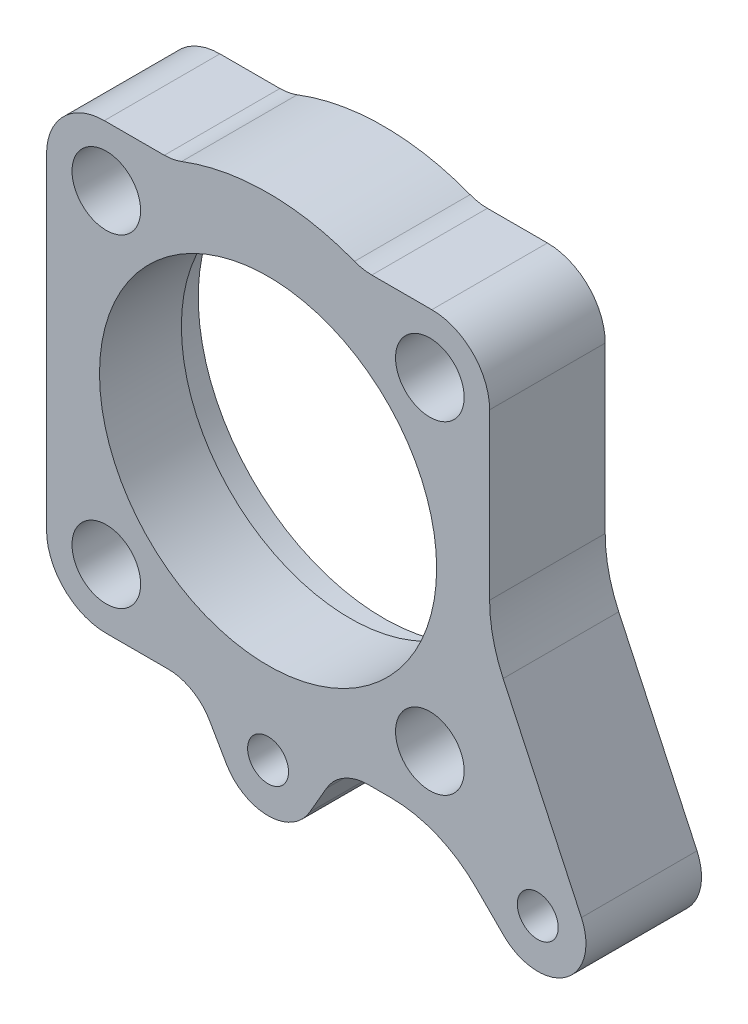
SolidWorks part; units mm, degrees
ref_plane "Front" through (0, 0, 0) normal (0, 0, 1) x (1, 0, 0)
ref_plane "Top" through (0, 0, 0) normal (0, 1, 0) x (1, 0, 0)
ref_plane "Right" through (0, 0, 0) normal (1, 0, 0) x (0, 0, -1)
sketch "Sketch1" plane through (0, 0, 0) normal (0, 0, 1) x (1, 0, 0)
  line L0 (-25.5577, 0) -> (31, 0) construction
  line L1 (0, 61.8389) -> (0, -52) construction
  line L2 (34, 46) -> (21.5407, 46)
  line L3 (46, 34) -> (46, -0.2421)
  line L4 (-33.5876, -46) -> (-20.7846, -46)
  line L5 (0, 0) -> (33.5876, 33.5876) construction
  line L6 (48.9289, -59.0711) -> (43.1802, -53.3223)
  line L7 (65.0631, -47.7738) -> (48.8108, -12.9206)
  line L9 (-46, -33.5876) -> (-46, 0)
  line L10 (8.6603, -57) -> (12.1244, -51)
  line L11 (-46, 34) -> (-46, 0)
  line L12 (-34, 46) -> (-21.5407, 46)
  line L13 (25.5025, -46) -> (20.7846, -46)
  line L14 (-8.6603, -57) -> (-12.1244, -51)
  circle A0 centre (0, 0) radius 31
  arc A1 (17.9505, 46.6667) -> (-17.9505, 46.6667) centre (0, 0) ccw
  arc A2 (8.6603, -57) -> (-8.6603, -57) centre (0, -52) cw
  arc A3 (65.0631, -47.7738) -> (48.9289, -59.0711) centre (56, -52) cw
  circle A4 centre (0, 0) radius 47.5 construction
  circle A5 centre (33.5876, 33.5876) radius 7.125 construction
  arc A6 (46, 34) -> (34, 46) centre (34, 34) ccw
  arc A7 (17.9505, 46.6667) -> (21.5407, 46) centre (21.5407, 56) ccw
  arc A8 (25.5025, -46) -> (43.1802, -53.3223) centre (25.5025, -71) cw
  arc A9 (-46, -33.5876) -> (-33.5876, -46) centre (-33.5876, -33.5876) ccw
  circle A10 centre (33.5876, -33.5876) radius 7.125 construction
  arc A11 (46, -0.2421) -> (48.8108, -12.9206) centre (76, -0.2421) ccw
  arc A13 (20.7846, -46) -> (12.1244, -51) centre (20.7846, -56) ccw
  arc A14 (-20.7846, -46) -> (-12.1244, -51) centre (-20.7846, -56) cw
  circle A16 centre (-33.5876, -33.5876) radius 7.125 construction
  arc A19 (-17.9505, 46.6667) -> (-21.5407, 46) centre (-21.5407, 56) cw
  arc A20 (-46, 34) -> (-34, 46) centre (-34, 34) cw
  circle A21 centre (-33.5876, 33.5876) radius 7.125 construction
  point P41 (15.0111, -46)
  point P47 (-15.0111, -46)
  dimension "D1" = 62
  dimension "D2" = 50
  dimension "D6" = 10
  dimension "D8" = 56
  dimension "D9" = 95
  dimension "D10" = 45
  dimension "D11" = 14.25
  dimension "D12" = 12
  dimension "D13" = 10
  dimension "D4" = 52
  dimension "D14" = 30
  dimension "D15" = 65
  dimension "D16" = 10
  dimension "D18" = 25
  dimension "D3" = 46
  dimension "D5" = 60
  dimension "D7" = 92
  dimension "D17" = 45
extrude "Base-Extrude" add sketch "Sketch1" along normal mid plane 24
sketch "Sketch2" plane through (0, 0, 0) normal (1, 0, 0) x (0, 0, -1)
  line L0 (0, 0) -> (40.5123, 0) construction
  line L1 (-12, 0) -> (12, 0) construction
  line L2 (12, 38.5) -> (5, 38.5)
  line L3 (-12, 34) -> (-12, -0.2421) construction
  line L4 (12, 34) -> (12, -0.2421) construction
  line L5 (5, 38.5) -> (5, 35)
  line L6 (5, 35) -> (-12, 35)
  line L7 (12, 38.5) -> (12, 0)
  line L8 (12, 0) -> (-12, 0)
  line L9 (-12, 0) -> (-12, 35)
  dimension "D1" = 7
  dimension "D3" = 70
  dimension "D4" = 77
revolve "Uddrejning" cut sketch "Sketch2" angle 360 about L0
hole_wizard "M10 gevindhuller" positions "Sketch6" profile "Sketch5" legacy end condition through all
sketch "Sketch6" plane through (0, 0, 12) normal (0, 0, 1) x (1, 0, 0)
  arc A0 (-8.6603, -57) -> (8.6603, -57) centre (0, -52) ccw construction
  arc A1 (48.9289, -59.0711) -> (65.0631, -47.7738) centre (56, -52) ccw construction
  point P0 (56, -52)
  point P3 (0, -52)
sketch "Sketch5" plane through (56, -52, 12) normal (1, 0, 0) x (0, -1, 0)
  line L0 (0, 0) -> (0, 26.5537)
  line L1 (0, 26.5537) -> (4.25, 24)
  line L2 (4.25, 24) -> (4.25, 0)
  line L4 (4.25, 0) -> (0, 0)
  line L6 (0, 26.5537) -> (-4.25, 24) construction
  line L7 (0, -4.2442) -> (0, 117.3081) construction
  dimension "Diameter" = 8.5
  dimension "Depth" = 24
  dimension "Drill Angle" = 118
cosmetic thread "Cosmetic Thread1" parameters "D2"=10
cosmetic thread "Cosmetic Thread2" parameters "D2"=10
sketch "Sketch7" plane through (0, 0, 12) normal (0, 0, 1) x (1, 0, 0)
  circle A0 centre (33.5876, 33.5876) radius 7.125 construction
  circle A1 centre (33.5876, -33.5876) radius 7.125 construction
  circle A2 centre (-33.5876, -33.5876) radius 7.125 construction
  circle A3 centre (-33.5876, 33.5876) radius 7.125 construction
  circle A4 centre (33.5876, 33.5876) radius 7.125
  circle A5 centre (33.5876, -33.5876) radius 7.125
  circle A6 centre (-33.5876, -33.5876) radius 7.125
  circle A7 centre (-33.5876, 33.5876) radius 7.125
extrude "ø14.25 huller" cut sketch "Sketch7" against normal through all
